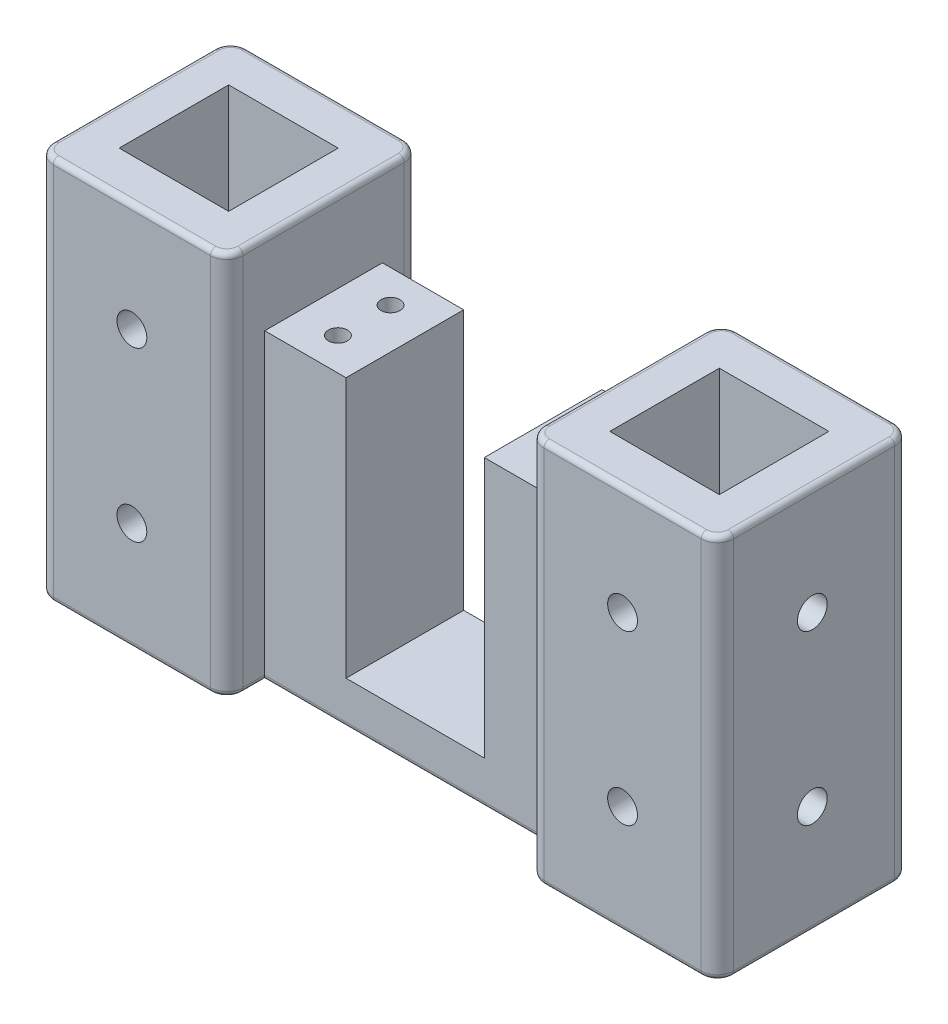
SolidWorks part; units mm, degrees
material "PETG"
ref_plane "Front Plane" through (0, 0, 0) normal (0, 0, 1) x (1, 0, 0)
ref_plane "Top Plane" through (0, 0, 0) normal (0, 1, 0) x (1, 0, 0)
ref_plane "Right Plane" through (0, 0, 0) normal (1, 0, 0) x (0, 0, -1)
sketch "Sketch1" plane through (0, 0, 0) normal (0, 0, 1) x (1, 0, 0)
  line L0 (27.75, 0) -> (-27.75, 0)
  line L1 (-27.75, 0) -> (-27.75, 56)
  line L2 (-27.75, 56) -> (-12.75, 56)
  line L3 (-12.75, 56) -> (-12.75, 8)
  line L4 (-12.75, 8) -> (12.75, 8)
  line L5 (0, 287.7708) -> (0, -102.5473) construction
  line L6 (27.75, 0) -> (27.75, 56)
  line L7 (27.75, 56) -> (12.75, 56)
  line L8 (12.75, 56) -> (12.75, 8)
  point P10 (0, 0)
  point P13 (0, 8)
  dimension "D1" = 25.5
  dimension "D2" = 15
  dimension "D3" = 8
  dimension "D4" = 48
extrude "Boss-Extrude1" add sketch "Sketch1" along normal blind 21.7
sketch "Sketch2" plane through (0, 56, 0) normal (0, 1, 0) x (1, 0, 0)
  line L0 (20.25, 0) -> (20.25, -21.7) construction
  line L1 (27.75, 0) -> (12.75, 0) construction
  line L3 (12.75, -21.7) -> (12.75, 0) construction
  line L4 (12.75, -10.85) -> (27.75, -10.85) construction
  line L5 (27.75, -21.7) -> (27.75, 0) construction
  line L6 (0, 9.752) -> (0, -29.1441) construction
  line L7 (27.75, -21.7) -> (12.75, -21.7) construction
  circle A0 centre (20.25, -6) radius 1.75
  circle A11 centre (20.25, -15.7) radius 1.75
  circle A12 centre (-20.25, -15.7) radius 1.75
  circle A13 centre (-20.25, -6) radius 1.75
  dimension "D1" = 3.5
  dimension "D3" = 6
extrude "Cut-Extrude1" cut sketch "Sketch2" against normal blind 10
sketch "Sketch3" plane through (27.75, 0, 0) normal (1, 0, 0) x (0, 0, -1)
  line L0 (-21.7, 28) -> (0, 28) construction
  line L1 (-21.7, 56) -> (0, 56) construction
  line L2 (-21.7, 56) -> (-21.7, 0) construction
  line L3 (-21.7, 0) -> (0, 0) construction
  line L4 (0, 56) -> (0, 0) construction
  line L5 (-28.7, 71) -> (7, 71)
  line L6 (-28.7, 71) -> (-28.7, 0)
  line L7 (-28.7, 0) -> (7, 0)
  line L8 (7, 71) -> (7, 0)
  line L9 (-28.7, 71) -> (7, 0) construction
  line L10 (-28.7, 0) -> (7, 71) construction
  line L11 (-10.85, 56) -> (-10.85, 0) construction
  point P8 (-10.85, 35.5)
  dimension "D1" = 15
  dimension "D3" = 7
  dimension "D4" = 7
extrude "Boss-Extrude2" add sketch "Sketch3" along normal blind 35
mirror "Mirror1" about plane through (0, 0, 0) normal (1, 0, 0) of "Boss-Extrude2"
sketch "Sketch4" plane through (0, 0, 0) normal (0, -1, 0) x (1, 0, 0)
  line L0 (27.75, 28.7) -> (62.75, -7) construction
  line L1 (27.75, 28.7) -> (62.75, 28.7) construction
  line L2 (27.75, 28.7) -> (27.75, -7) construction
  line L3 (27.75, -7) -> (62.75, -7) construction
  line L4 (62.75, 28.7) -> (62.75, -7) construction
  line L5 (27.75, -7) -> (62.75, 28.7) construction
  line L7 (35.15, 0.75) -> (55.35, 0.75)
  line L8 (35.15, 0.75) -> (35.15, 20.95)
  line L9 (35.15, 20.95) -> (55.35, 20.95)
  line L10 (55.35, 0.75) -> (55.35, 20.95)
  line L11 (35.15, 0.75) -> (55.35, 20.95) construction
  line L12 (35.15, 20.95) -> (55.35, 0.75) construction
  point P6 (45.25, 10.85)
  dimension "D1" = 20.2
extrude "Cut-Extrude2" cut sketch "Sketch4" against normal through all
mirror "Mirror2" about plane through (0, 0, 0) normal (1, 0, 0) of "Cut-Extrude2"
sketch "Sketch5" plane through (0, 0, 28.7) normal (0, 0, 1) x (1, 0, 0)
  line L0 (45.25, 71) -> (45.25, 0) construction
  line L1 (62.75, 71) -> (27.75, 71) construction
  line L2 (62.75, 0) -> (27.75, 0) construction
  line L3 (27.75, 35.5) -> (62.75, 35.5) construction
  line L4 (27.75, 71) -> (27.75, 0) construction
  line L5 (62.75, 71) -> (62.75, 0) construction
  circle A0 centre (45.25, 51) radius 2.75
  circle A1 centre (45.25, 20) radius 2.75
  dimension "D1" = 5.5
  dimension "D2" = 20
extrude "Cut-Extrude3" cut sketch "Sketch5" against normal blind 10
mirror "Mirror3" about plane through (0, 0, 0) normal (1, 0, 0) of "Cut-Extrude3"
ref_plane "Plane1" through (17.649, 0, -17.303) normal (0.7141, 0, -0.7001) x (-0.7001, 0, -0.7141)
mirror "Mirror4" about plane through (17.649, 0, -17.303) normal (0.7141, 0, -0.7001) of "Cut-Extrude3"
ref_plane "Plane2" through (-17.649, 0, -17.303) normal (-0.7141, 0, -0.7001) x (-0.7001, 0, 0.7141)
mirror "Mirror5" about plane through (-17.649, 0, -17.303) normal (-0.7141, 0, -0.7001) of "Mirror3"
ref_plane "Plane3" through (0, 0, 10.85) normal (0, 0, -1) x (-1, 0, 0)
mirror "Mirror6" about plane through (0, 0, 10.85) normal (0, 0, -1) of "Mirror3", "Cut-Extrude3"
fillet "Fillet1" radius 3 8 edges at (-62.75, 35.5, 28.7) (-27.75, 35.5, 28.7) (27.75, 35.5, 28.7) (62.75, 35.5, 28.7) (62.75, 35.5, -7) (27.75, 35.5, -7) (-27.75, 35.5, -7) (-62.75, 35.5, -7)
fillet "Fillet2" radius 1 36 edges at (-61.8713, 71, 27.8213) (-62.75, 71, 10.85) (-61.8713, 71, -6.1213) (-45.25, 71, -7) (-28.6287, 71, -6.1213) (-27.75, 71, 10.85) (-28.6287, 71, 27.8213) (61.8713, 71, -6.1213) (45.25, 71, -7) (28.6287, 71, -6.1213) (27.75, 71, 10.85) (28.6287, 71, 27.8213) (45.25, 71, 28.7) (61.8713, 71, 27.8213) (-27.75, 0, 23.7) (-28.6287, 0, 27.8213) (-45.25, 71, 28.7) (-45.25, 0, 28.7) (-61.8713, 0, 27.8213) (-62.75, 0, 10.85) (-61.8713, 0, -6.1213) (-27.75, 0, -2) (-28.6287, 0, -6.1213) (27.75, 0, 23.7) (28.6287, 0, 27.8213) (45.25, 0, 28.7) (61.8713, 0, 27.8213) (62.75, 0, 10.85) (61.8713, 0, -6.1213) (27.75, 0, -2) (28.6287, 0, -6.1213) (62.75, 71, 10.85) (-45.25, 0, -7) (0, 0, 0) (0, 0, 21.7) (45.25, 0, -7)
